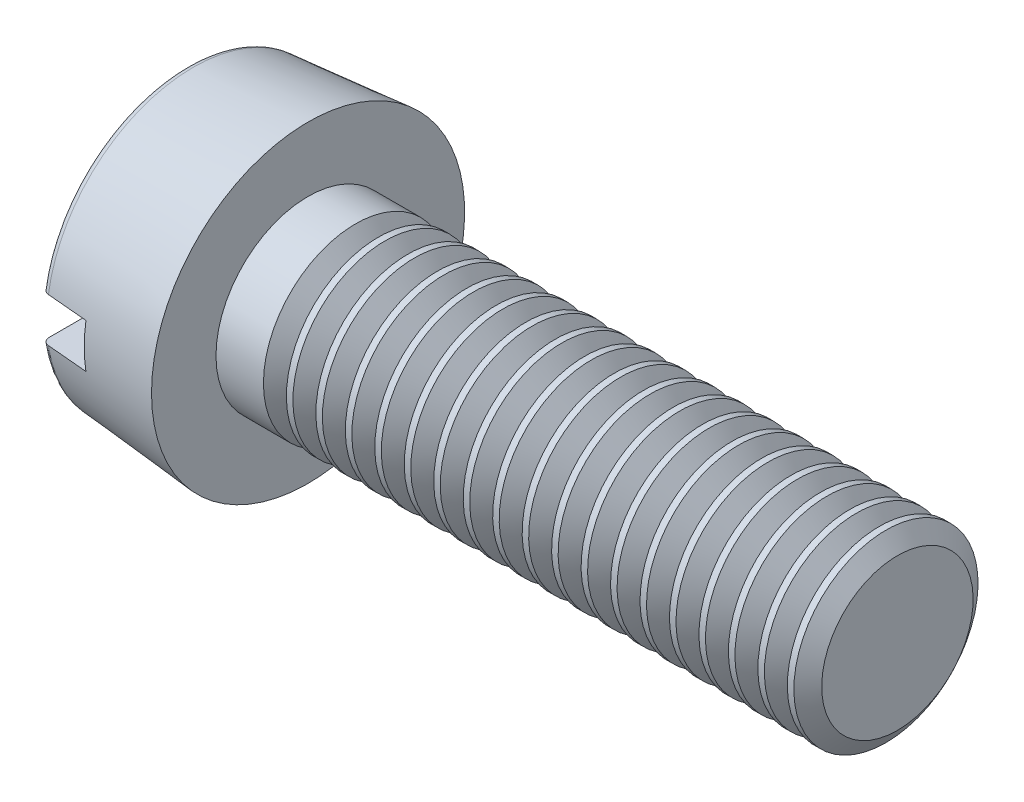
SolidWorks part; units mm, degrees
ref_plane "Plane1" through (0, 0, 0) normal (0, 0, 1) x (1, 0, 0)
ref_plane "Plane2" through (0, 0, 0) normal (0, 1, 0) x (1, 0, 0)
ref_plane "Plane3" through (0, 0, 0) normal (1, 0, 0) x (0, 0, -1)
sketch "BodySke" plane through (0, 0, 0) normal (0, 0, 1) x (1, 0, 0)
  line L0 (3.3, 2.5) -> (3.3, 4.25)
  line L1 (0, 0) -> (0, 3.9613)
  line L2 (-25.4, 0) -> (127, 0) construction
  line L3 (19.3, 0) -> (0, 0)
  line L4 (3.3, 2.5) -> (19.3, 2.5)
  line L5 (19.3, 2.5) -> (19.3, 0)
  line L6 (0, 3.9613) -> (3.3, 4.25)
  line L9 (4.1, 4.0875) -> (4.1, -5.4375) construction
  line L10 (3.3, 6.35) -> (3.3, -3.175) construction
  dimension "Head_ht" = 3.3
  dimension "Diameter" = 5
  dimension "Length" = 16
  dimension "Head_dia" = 8.5
  dimension "Advance" = 0.8
  dimension "Thread_nom" = 16
  dimension "Head_side_angle" = 5
revolve "Base-Revolve" add sketch "BodySke"
cosmetic thread "ThreadCosmetic" [suppressed]
fillet "Fillet1" [suppressed] radius 0.2
fillet "Fillet2" radius 0.2 1 edges at (0, 0, 3.9613)
sketch "Sketch2" plane through (0, 0, 0) normal (1, 0, 0) x (0, 0, -1)
  line L0 (4.25, -0.6) -> (-4.25, -0.6)
  line L1 (4.25, -0.6) -> (4.25, 0.6)
  line L2 (-4.25, 0.6) -> (4.25, 0.6)
  line L3 (-4.25, 0.6) -> (-4.25, -0.6)
  dimension "D1" = 8.5
  dimension "D2" = 4.25
  dimension "Slot_width" = 1.2
  dimension "D3" = 0.6
extrude "Slot" cut sketch "Sketch2" along normal blind 1.3
sketch "ThdSchSke" plane through (0, 0, 0) normal (0, 0, 1) x (1, 0, 0)
  line L0 (4.9, -2.055) -> (4.5884, -2.5)
  line L1 (4.9, -2.055) -> (5.2116, -2.5)
  line L2 (5.2116, -2.5) -> (5.2116, -3.125)
  line L3 (-3.175, 0) -> (5.1513, 0) construction
  line L5 (5.2116, -3.125) -> (4.5884, -3.125)
  line L6 (4.5884, -3.125) -> (4.5884, -2.5)
  dimension "Thread_minor" = 4.11
  dimension "Diameter" = 5
  dimension "Start" = 4.9
  dimension "SideAngle" = 55
  dimension "VeeAngle" = 70
  dimension "Overcut" = 6.25
revolve "ThreadSchematic" cut sketch "ThdSchSke" angle 360 about L3
pattern_linear "ThdSchPat" count 19 spacing 0.8 along (1, 0, 0) of "ThreadSchematic"
equation "\"D1@Sketch2\" = \"Head_dia@BodySke\""
equation "\"D2@Sketch2\" = \"D1@Sketch2\" / 2"
equation "\"D3@Sketch2\" = \"Slot_width@Sketch2\" / 2"
equation "\"Thread_length@ThreadCosmetic\" = ((sgn( (\"Length@BodySke\" - \"Advance@BodySke\" * 2.0 ) - \"Thread_nom@BodySke\" )-1)*( (\"Length@BodySke\" - \"Advance@BodySke\"  * 2.0) - \"Thread_nom@BodySke\" ))/-2+ \"Thread_nom@BodySke\""
equation "\"Thread_minor@ThdSchSke\" = \"Thread_minor@ThreadCosmetic\""
equation "\"Diameter@ThdSchSke\" = \"Diameter@BodySke\""
equation "\"Overcut@ThdSchSke\" = \"Diameter@BodySke\" * 1.25"
equation "\"Start@ThdSchSke\" = \"Head_ht@BodySke\" + \"Length@BodySke\" - \"Thread_length@ThreadCosmetic\"  '---Non-countersunk---"
equation "\"Num_threads@ThdSchPat\" = int( \"Thread_length@ThreadCosmetic\" / \"Advance@BodySke\" + 0.999 )  + 1"
equation "\"Advance@ThdSchPat\" = \"Thread_length@ThreadCosmetic\" /  (\"Num_threads@ThdSchPat\" - 1) 'relax it"
